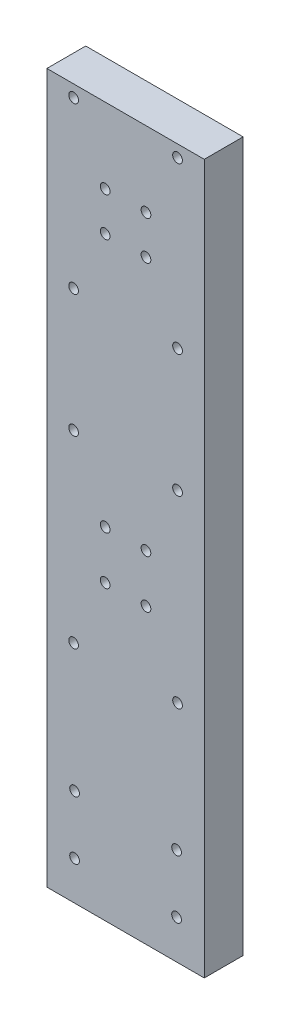
SolidWorks part; units mm, degrees
ref_plane "Front Plane" through (0, 0, 0) normal (0, 0, 1) x (1, 0, 0)
ref_plane "Top Plane" through (0, 0, 0) normal (0, 1, 0) x (1, 0, 0)
ref_plane "Right Plane" through (0, 0, 0) normal (1, 0, 0) x (0, 0, -1)
sketch "Sketch1" plane through (0, 0, 0) normal (0, 0, 1) x (1, 0, 0)
  line L0 (0, 44.76) -> (16.2, 44.76) construction
  line L1 (0, 12.5) -> (16.2, 12.5) construction
  line L2 (0, 20.5) -> (16.2, 20.5) construction
  line L4 (0, 0) -> (0, 72.99)
  line L5 (0, 0) -> (16.2, 0)
  line L6 (0, 72.99) -> (16.2, 72.99)
  line L7 (16.2, 72.99) -> (16.2, 0)
  line L8 (0, 52.76) -> (16.2, 52.76) construction
  circle A16 centre (6, 30.15) radius 0.5
  circle A17 centre (10.2, 30.15) radius 0.5
  circle A18 centre (10.2, 35.11) radius 0.5
  circle A19 centre (10.2, 61.26) radius 0.5
  circle A20 centre (13.45, 54.76) radius 0.5
  circle A21 centre (6, 61.26) radius 0.5
  circle A22 centre (6, 35.11) radius 0.5
  circle A23 centre (2.75, 42.11) radius 0.5
  circle A24 centre (2.85, 10) radius 0.5
  circle A25 centre (13.35, 10) radius 0.5
  circle A26 centre (13.35, 4) radius 0.5
  circle A27 centre (2.85, 4) radius 0.5
  circle A28 centre (13.45, 42.11) radius 0.5
  circle A29 centre (2.75, 54.76) radius 0.5
  circle A30 centre (13.45, 23.15) radius 0.5
  circle A31 centre (2.75, 23.15) radius 0.5
  circle A32 centre (10.2, 65.26) radius 0.5
  circle A33 centre (13.45, 71.76) radius 0.5
  circle A34 centre (6, 65.26) radius 0.5
  circle A35 centre (2.75, 71.76) radius 0.5
  dimension "D1" = 2.85
  dimension "D2" = 2.85
  dimension "D3" = 16.2
  dimension "D4" = 4
  dimension "D5" = 4
  dimension "D6" = 6
  dimension "D7" = 6
  dimension "D8" = 2.85
  dimension "D9" = 2.85
  dimension "D10" = 2.5
  dimension "D11" = 8
  dimension "D12" = 24.26
  dimension "D13" = 8
  dimension "D14" = 2.75
  dimension "D15" = 6
  dimension "D16" = 2.65
  dimension "D17" = 9.65
  dimension "D18" = 2.75
  dimension "D19" = 6
  dimension "D20" = 2.65
  dimension "D21" = 9.65
  dimension "D22" = 2.75
  dimension "D23" = 2.75
  dimension "D24" = 6
  dimension "D25" = 6
  dimension "D26" = 2.65
  dimension "D27" = 9.65
  dimension "D28" = 9.65
  dimension "D29" = 2.65
  dimension "D30" = 20.23
  dimension "D31" = 2.75
  dimension "D32" = 6
  dimension "D33" = 2
  dimension "D34" = 8.5
  dimension "D35" = 4
  dimension "D36" = 6.5
  dimension "D37" = 2.75
  dimension "D38" = 6
  dimension "D39" = 2.75
  dimension "D40" = 6
  dimension "D41" = 2
  dimension "D42" = 8.5
  dimension "D43" = 4
  dimension "D44" = 6.5
  dimension "D45" = 6
  dimension "D46" = 2.75
extrude "Boss-Extrude1" add sketch "Sketch1" along normal blind 4
equation "\"D12@Sketch1\"= \"HL@parametersSketch@prostheticParameters.SLDPRT\" * 0.196 - 4 - 8'Thumb PIP Length"
equation "\"D30@Sketch1\"= \"HL@parametersSketch@prostheticParameters.SLDPRT\" * 0.158 - 4 - 5'Thumb DIP Length - Fingertip"
equation "\"D3@Sketch1\"= \"fingerWidth@parametersSketch@prostheticParameters.SLDPRT\"'Thumb Breadth"
